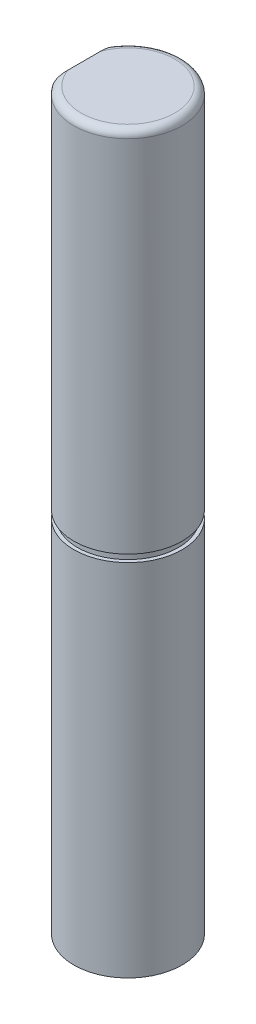
SolidWorks part; units mm, degrees
ref_plane "前视基准面" through (0, 0, 0) normal (0, 0, 1) x (1, 0, 0)
ref_plane "上视基准面" through (0, 0, 0) normal (0, 1, 0) x (1, 0, 0)
ref_plane "右视基准面" through (0, 0, 0) normal (1, 0, 0) x (0, 0, -1)
sketch "草图1" plane through (0, 0, 0) normal (0, 1, 0) x (1, 0, 0)
  circle A0 centre (0, 0) radius 1.475
  dimension "D1" = 2.95
extrude "凸台-拉伸1" add sketch "草图1" along normal blind 20
ref_plane "基准面1" through (0, 10, 0) normal (0, 1, 0) x (1, 0, 0)
sketch "草图2" plane through (0, 10, 0) normal (0, 1, 0) x (1, 0, 0)
  circle A0 centre (0, 0) radius 1.475
  circle A1 centre (0, 0) radius 1.475 construction
extrude "切除-拉伸-薄壁4" cut sketch "草图2" against normal blind 0.2 thin thin type one direction reverse wall 0.1
sketch "草图3" plane through (0, 20, 0) normal (0, 1, 0) x (1, 0, 0)
  line L0 (-1.195, 0.8646) -> (-1.195, -0.8646)
  line L1 (1.475, 1.1403) -> (1.475, -1.7543) construction
  circle A0 centre (0, 0) radius 1.475 construction
  arc A1 (-1.195, 0.8646) -> (-1.195, -0.8646) centre (0, 0) ccw
  dimension "D1" = 2.67
extrude "切除-拉伸1" cut sketch "草图3" against normal blind 7.42
fillet "圆角1" radius 0.2 1 edges at (1.475, 20, 0)
